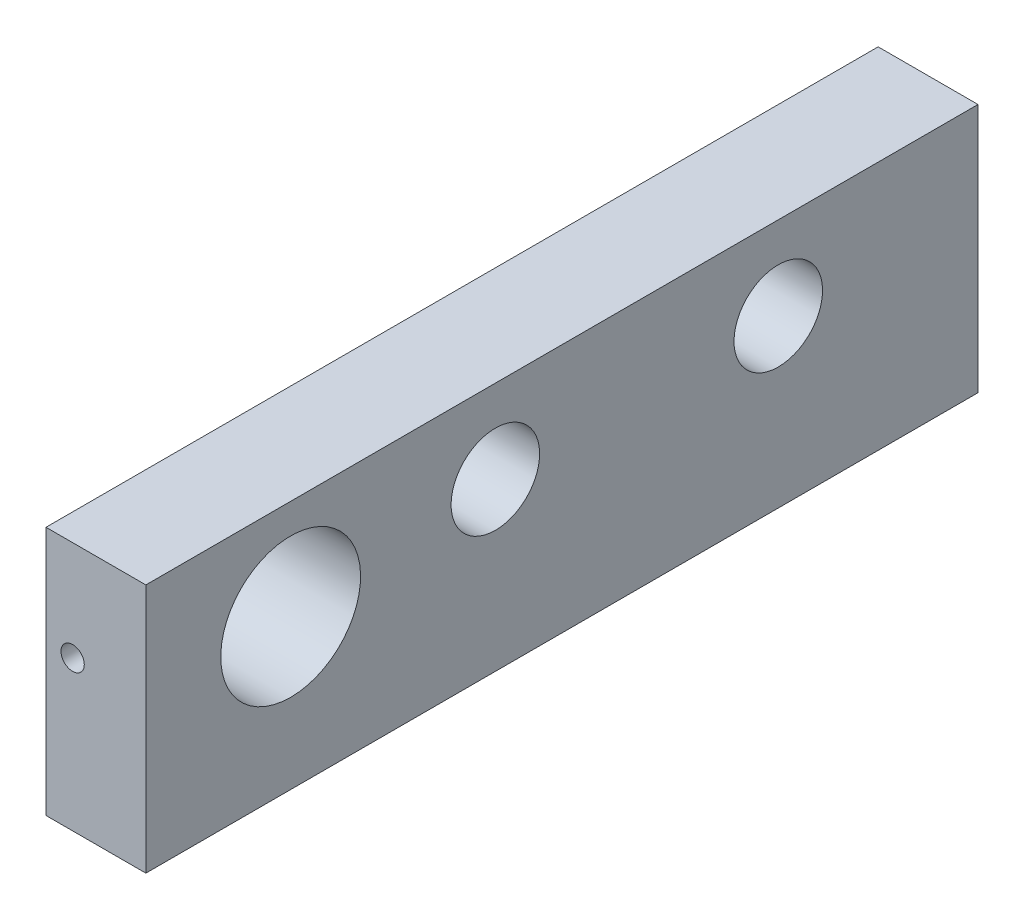
SolidWorks part; units mm, degrees
ref_plane "Front Plane" through (0, 0, 0) normal (0, 0, 1) x (1, 0, 0)
ref_plane "Top Plane" through (0, 0, 0) normal (0, 1, 0) x (1, 0, 0)
ref_plane "Right Plane" through (0, 0, 0) normal (1, 0, 0) x (0, 0, -1)
sketch "Sketch1" plane through (0, 0, 0) normal (0, 0, 1) x (1, 0, 0)
  line L1 (0, 0) -> (7.62, 0)
  line L2 (0, 0) -> (0, 19.05)
  line L3 (0, 19.05) -> (7.62, 19.05)
  line L4 (7.62, 0) -> (7.62, 19.05)
  dimension "D1" = 7.62
  dimension "D2" = 19.05
extrude "Boss-Extrude1" add sketch "Sketch1" against normal blind 63.5
sketch "Sketch2" plane through (0, 0, 0) normal (0, 0, 1) x (1, 0, 0)
  line L0 (0, 19.05) -> (0, 0) construction
  line L1 (0, 0) -> (7.62, 0) construction
  circle A0 centre (2.032, 11.43) radius 0.889
  dimension "D3" = 1.778
  dimension ".08" = 2.032
  dimension "D2" = 11.43
extrude "Cut-Extrude1" cut sketch "Sketch2" against normal blind 6.35
sketch "Sketch3" plane through (0, 0, 0) normal (-1, 0, 0) x (0, 0, 1)
  line L0 (-63.5, 19.05) -> (-63.5, 0) construction
  line L1 (-63.5, 0) -> (0, 0) construction
  circle A0 centre (-48.26, 12.7) radius 3.3782
  dimension "D1" = 6.7564
  dimension "D2" = 15.24
  dimension "D3" = 12.7
extrude "Cut-Extrude2" cut sketch "Sketch3" against normal through all
sketch "Sketch4" plane through (0, 0, 0) normal (-1, 0, 0) x (0, 0, 1)
  line L0 (-63.5, 0) -> (0, 0) construction
  line L1 (-63.5, 19.05) -> (-63.5, 0) construction
  circle A0 centre (-26.67, 12.7) radius 3.3782
  dimension "D2" = 6.7564
  dimension "D1" = 12.7
  dimension "D3" = 36.83
extrude "Cut-Extrude3" cut sketch "Sketch4" against normal through all
sketch "Sketch5" plane through (0, 0, 0) normal (-1, 0, 0) x (0, 0, 1)
  line L0 (-63.5, 19.05) -> (-63.5, 0) construction
  line L1 (-63.5, 0) -> (0, 0) construction
  circle A0 centre (-11.049, 11.43) radius 5.334
  dimension "D2" = 10.668
  dimension "D3" = 11.43
  dimension "D1" = 52.451
extrude "Cut-Extrude4" cut sketch "Sketch5" against normal through all
